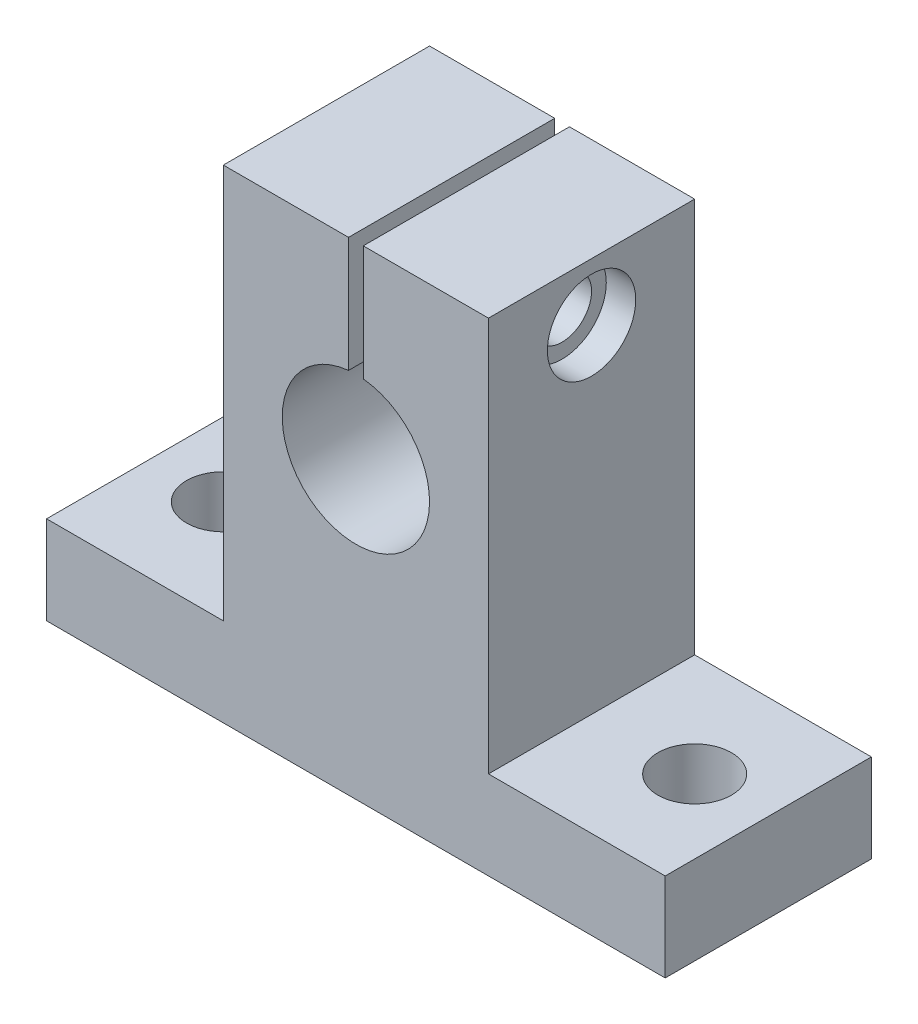
SolidWorks part; units mm, degrees
ref_plane "前视基准面" through (0, 0, 0) normal (0, 0, 1) x (1, 0, 0)
ref_plane "上视基准面" through (0, 0, 0) normal (0, 1, 0) x (1, 0, 0)
ref_plane "右视基准面" through (0, 0, 0) normal (1, 0, 0) x (0, 0, -1)
sketch "草图1" plane through (0, 0, 0) normal (0, 0, 1) x (1, 0, 0)
  line L0 (0, 0) -> (0, 255.3694) construction
  line L1 (21, 0) -> (-21, 0)
  line L2 (-21, 0) -> (-21, 6)
  line L3 (-21, 6) -> (-9, 6)
  line L4 (-9, 6) -> (-9, 32.8)
  line L5 (-9, 32.8) -> (9, 32.8)
  line L6 (21, 0) -> (21, 6)
  line L7 (9, 6) -> (9, 32.8)
  line L8 (21, 6) -> (9, 6)
  circle A0 centre (0, 20) radius 5
  point P13 (0, 32.8)
  dimension "D5" = 10
  dimension "D1" = 21
  dimension "D2" = 6
  dimension "D3" = 32.8
  dimension "D4" = 18
  dimension "D6" = 20
extrude "凸台-拉伸1" add sketch "草图1" along normal blind 14
sketch "草图2" plane through (0, 6, 0) normal (0, 1, 0) x (1, 0, 0)
  line L0 (-21, -7) -> (-9, -7) construction
  line L1 (-21, -14) -> (-21, 0) construction
  line L2 (-9, -14) -> (-9, 0) construction
  line L3 (0, 0) -> (0, -14) construction
  line L4 (9, -14) -> (-9, -14) construction
  circle A0 centre (-16, -7) radius 2.5
  circle A1 centre (16, -7) radius 2.5
  dimension "D1" = 5
  dimension "D2" = 5
extrude "切除-拉伸1" cut sketch "草图2" against normal through all
sketch "草图3" plane through (0, 32.8, 0) normal (0, 1, 0) x (1, 0, 0)
  line L0 (0, 0) -> (0, -14) construction
  line L1 (9, 0) -> (-9, 0) construction
  line L2 (9, -14) -> (-9, -14) construction
  line L4 (-0.5, 0) -> (0.5, 0)
  line L5 (-0.5, 0) -> (-0.5, -14)
  line L6 (-0.5, -14) -> (0.5, -14)
  line L7 (0.5, 0) -> (0.5, -14)
  dimension "D1" = 1
extrude "切除-拉伸2" cut sketch "草图3" against normal blind 14
sketch "草图4" plane through (-0.5, 0, 0) normal (1, 0, 0) x (0, 0, -1)
  line L0 (-14, 24.9749) -> (0, 24.9749) construction
  line L1 (-14, 24.9749) -> (0, 24.9749) construction
  line L2 (-7, 24.9749) -> (-7, 32.8) construction
  line L3 (-14, 32.8) -> (0, 32.8) construction
  circle A0 centre (-7, 28.8875) radius 2
  dimension "D1" = 4
extrude "切除-拉伸3" cut sketch "草图4" against normal mid plane 20
sketch "草图5" plane through (9, 0, 0) normal (1, 0, 0) x (0, 0, -1)
  circle A0 centre (-7, 28.8875) radius 3
  dimension "D1" = 6
extrude "切除-拉伸4" cut sketch "草图5" against normal blind 2
